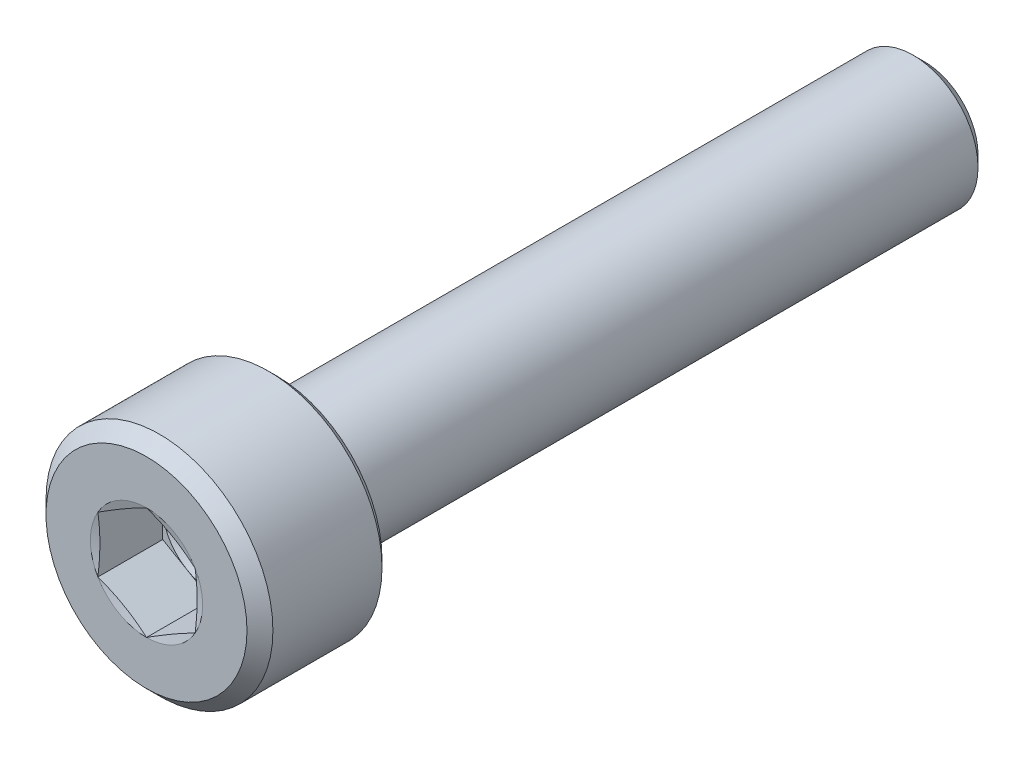
SolidWorks part; units mm, degrees
ref_plane "Front Plane" through (0, 0, 0) normal (0, 0, 1) x (1, 0, 0)
ref_plane "Top Plane" through (0, 0, 0) normal (0, 1, 0) x (1, 0, 0)
ref_plane "Right Plane" through (0, 0, 0) normal (1, 0, 0) x (0, 0, -1)
sketch "Sketch1" plane through (0, 0, 0) normal (1, 0, 0) x (0, 0, -1)
  line L0 (0, 0) -> (12.9407, 0) construction
  line L1 (0, 0) -> (0, 3.1)
  line L2 (0, 3.1) -> (0.4, 3.5)
  line L3 (0.4, 3.5) -> (3.765, 3.5)
  line L4 (4, 3.265) -> (4, 2.35)
  line L5 (4.6, 2) -> (23.65, 2)
  line L6 (23.65, 2) -> (24, 1.65)
  line L7 (24, 1.65) -> (24, 0)
  line L8 (24, 0) -> (0, 0)
  line L9 (3.765, 3.5) -> (4, 3.265)
  line L10 (4.5298, 2.0127) -> (4.1298, 2.1627)
  arc A2 (4.6, 2) -> (4.5298, 2.0127) centre (4.6, 2.2) cw
  arc A3 (4.1298, 2.1627) -> (4, 2.35) centre (4.2, 2.35) cw
  point P6 (4, 3.5)
  dimension "R2" = 0.2
  dimension "R1" = 0.2
  dimension "D1" = 45
  dimension "DK" = 7
  dimension "D3" = 45
  dimension "length" = 20
  dimension "K" = 4
  dimension "V" = 0.4
  dimension "HOLESIZE" = 4
  dimension "D4" = 3.3
  dimension "D5" = 45
  dimension "DW" = 6.53
  dimension "F" = 0.6
  dimension "DA" = 4.7
revolve "Revolve1" add sketch "Sketch1" angle 360 about L0
cosmetic thread "Cosmetic Thread1" parameters "D1"=17.9, "D2"=4
sketch "Sketch2" plane through (0, 0, 0) normal (0, 0, 1) x (1, 0, 0)
  line L0 (0, 0) -> (0, 1.7321) construction
  line L2 (0, 1.7321) -> (-1.5, 0.866)
  line L3 (-1.5, 0.866) -> (-1.5, -0.866)
  line L4 (-1.5, -0.866) -> (0, -1.7321)
  line L5 (0, -1.7321) -> (1.5, -0.866)
  line L6 (1.5, -0.866) -> (1.5, 0.866)
  line L7 (1.5, 0.866) -> (0, 1.7321)
  circle A0 centre (0, 0) radius 1.5 construction
  dimension "S" = 3
extrude "Cut-Extrude1" cut sketch "Sketch2" against normal blind 2
sketch "Sketch3" plane through (0, 0, 0) normal (1, 0, 0) x (0, 0, -1)
  line L0 (2, 0) -> (24, 0) construction
  line L1 (24, -1.65) -> (24, 1.65) construction
  line L2 (2, 0) -> (2, 1.5)
  line L4 (2, 1.5) -> (2.866, 0)
  line L5 (2.866, 0) -> (2, 0)
  line L6 (0, 3.1) -> (0, -3.1) construction
  dimension "DRILLANG" = 60
  dimension "DRILL DEPTH" = 2
  dimension "S2" = 3
revolve "Cut-Revolve2" cut sketch "Sketch3" angle 360 about L0
sketch "Sketch4" plane through (0, 0, 0) normal (1, 0, 0) x (0, 0, -1)
  line L0 (0, 0) -> (4.6121, 0) construction
  line L1 (0, 1.7321) -> (0, 1.5)
  line L2 (0, 3.1) -> (0, -3.1) construction
  line L3 (0, 1.5) -> (0.0622, 1.5)
  line L4 (0.0622, 1.5) -> (0, 1.7321)
  point P12 (0.0311, 1.5)
  dimension "D1" = 3
  dimension "D2" = 15
revolve "Cut-Revolve3" cut sketch "Sketch4" angle 360 about L0
